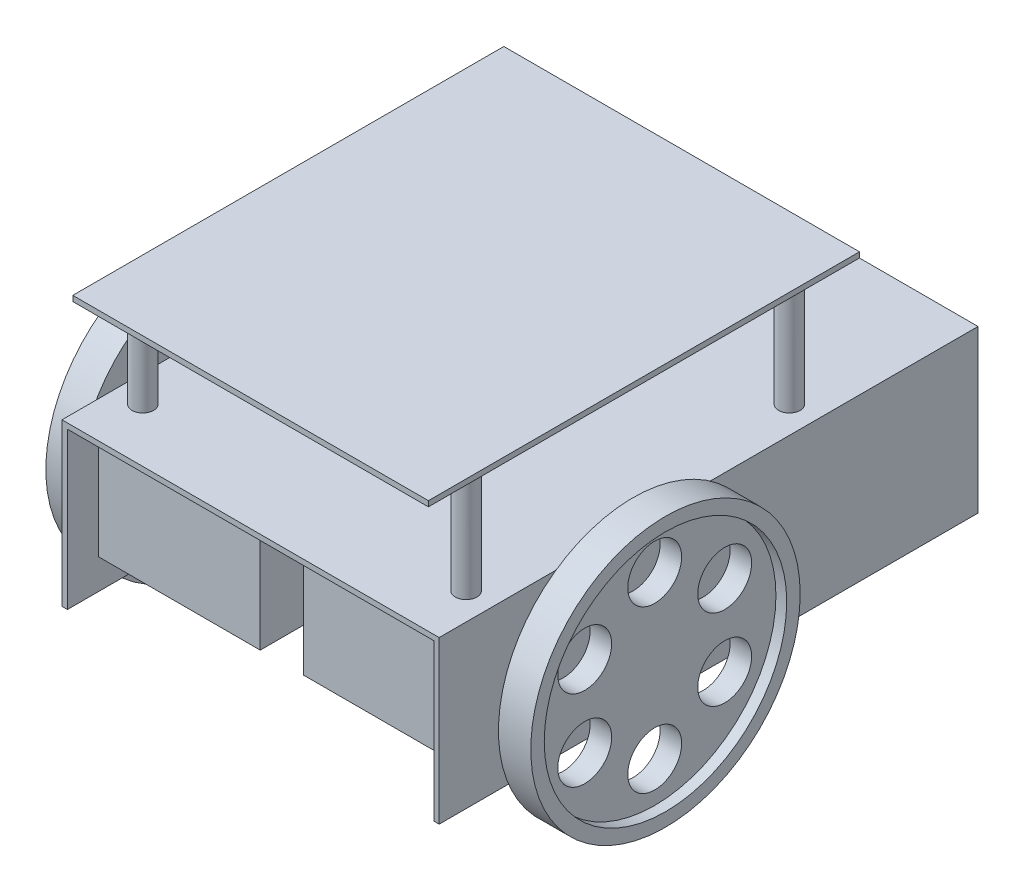
SolidWorks part; units mm, degrees
ref_plane "Front" through (0, 0, 0) normal (0, 0, 1) x (1, 0, 0)
ref_plane "Top" through (0, 0, 0) normal (0, 1, 0) x (1, 0, 0)
ref_plane "Right" through (0, 0, 0) normal (1, 0, 0) x (0, 0, -1)
sketch "草圖1" plane through (0, 0, 0) normal (0, 1, 0) x (1, 0, 0)
  line L1 (-35, 0) -> (35, 0)
  line L2 (-35, 0) -> (-35, 100)
  line L3 (-35, 100) -> (35, 100)
  line L4 (35, 0) -> (35, 100)
  dimension "D1" = 100
  dimension "D2" = 70
extrude "填料-伸長1" add sketch "草圖1" along normal blind 30
shell "薄殼1" thickness 1
sketch "草圖2" plane through (34, 0, 0) normal (-1, 0, 0) x (0, 0, 1)
  line L1 (-5.7932, 5.5786) -> (-45.7932, 5.5786)
  line L2 (-5.7932, 5.5786) -> (-5.7932, 25.5786)
  line L3 (-5.7932, 25.5786) -> (-45.7932, 25.5786)
  line L4 (-45.7932, 5.5786) -> (-45.7932, 25.5786)
  dimension "D1" = 40
  dimension "D2" = 20
extrude "填料-伸長2" add sketch "草圖2" along normal blind 30
sketch "草圖3" plane through (35, 0, 0) normal (1, 0, 0) x (0, 0, -1)
  line L0 (0, 0) -> (100, 0) construction
  line L1 (0, 30) -> (0, 0) construction
  circle A0 centre (32, 13.5) radius 1.5
  dimension "D1" = 13.5
  dimension "D2" = 32
  dimension "D3" = 3
extrude "填料-伸長3" add sketch "草圖3" along normal blind 10
sketch "草圖4" plane through (45, 0, 0) normal (1, 0, 0) x (0, 0, -1)
  circle A0 centre (32, 13.5) radius 25
  dimension "D1" = 50
extrude "填料-伸長4" add sketch "草圖4" against normal blind 6
sketch "草圖5" plane through (45, 0, 0) normal (1, 0, 0) x (0, 0, -1)
  circle A0 centre (32, 13.5) radius 22.5
  dimension "D1" = 45
extrude "除料-伸長1" cut sketch "草圖5" against normal blind 2
sketch "草圖6" plane through (43, 0, 0) normal (1, 0, 0) x (0, 0, -1)
  line L0 (32, 28.5) -> (32, 13.5) construction
  circle A0 centre (32, 28.5) radius 5
  dimension "D1" = 10
  dimension "D2" = 15
extrude "除料-伸長2" cut sketch "草圖6" against normal blind 8
pattern_circular "環狀複製排列1" count 6 over 360 about axis through (0, 13.5, -32) along (1, 0, 0) of "除料-伸長2"
mirror "鏡射1" about plane through (0, 0, 0) normal (1, 0, 0) of "填料-伸長2", "填料-伸長3", "填料-伸長4", "除料-伸長1", "除料-伸長2", "環狀複製排列1"
sketch "草圖9" plane through (0, 0, -100) normal (0, 0, -1) x (-1, 0, 0)
  line L0 (-35, 0) -> (35, 0) construction
  circle A0 centre (0, 0) radius 14
  dimension "D1" = 28
extrude "除料-伸長4" cut sketch "草圖9" against normal blind 8
sketch "草圖8" plane through (0, 0, -100) normal (0, 0, -1) x (-1, 0, 0)
  line L1 (34, 0) -> (31, 0)
  line L2 (34, 0) -> (34, 29)
  line L3 (34, 29) -> (31, 29)
  line L4 (31, 0) -> (31, 29)
  line L5 (-34, 0) -> (-31, 0)
  line L6 (-34, 0) -> (-34, 29)
  line L7 (-34, 29) -> (-31, 29)
  line L8 (-31, 0) -> (-31, 29)
  dimension "D1" = 3
  dimension "D2" = 3
extrude "除料-伸長3" cut sketch "草圖8" against normal blind 8
sketch "草圖7" plane through (0, 0, -100) normal (0, 0, -1) x (-1, 0, 0)
  line L0 (-35, 0) -> (-34, 0) construction
  line L1 (-12, 0) -> (12, 0)
  arc A0 (12, 0) -> (-12, 0) centre (0, 0) ccw
  dimension "D1" = 12
revolve "旋轉1" add sketch "草圖7" angle 360 about L1
sketch "草圖10" plane through (0, 0, 0) normal (1, 0, 0) x (0, 0, -1)
  line L0 (100, 30) -> (100, 0) construction
  circle A0 centre (100, 0) radius 1
  dimension "D1" = 2
extrude "填料-伸長5" add sketch "草圖10" along normal mid plane 28
sketch "草圖11" plane through (0, 30, 0) normal (0, 1, 0) x (1, 0, 0)
  line L0 (0, 40) -> (0, 0) construction
  line L1 (-30, 70) -> (30, 70) construction
  line L2 (-30, 70) -> (-30, 10) construction
  line L3 (-30, 10) -> (30, 10) construction
  line L4 (30, 70) -> (30, 10) construction
  line L5 (-30, 70) -> (30, 10) construction
  line L6 (-30, 10) -> (30, 70) construction
  circle A0 centre (30, 70) radius 2
  circle A1 centre (-30, 70) radius 2
  circle A2 centre (-30, 10) radius 2
  circle A3 centre (30, 10) radius 2
  point P0 (0, 40)
  dimension "D3" = 4
  dimension "D4" = 40
  dimension "D1" = 60
  dimension "D2" = 60
extrude "填料-伸長6" add sketch "草圖11" along normal blind 20
sketch "草圖12" plane through (0, 50, 0) normal (0, 1, 0) x (1, 0, 0)
  line L0 (0, 40) -> (0, 0) construction
  line L1 (-33, 80) -> (33, 80)
  line L2 (-33, 80) -> (-33, 0)
  line L3 (-33, 0) -> (33, 0)
  line L4 (33, 80) -> (33, 0)
  line L5 (-33, 80) -> (33, 0) construction
  line L6 (-33, 0) -> (33, 80) construction
  point P0 (0, 40)
  dimension "D1" = 80
  dimension "D2" = 66
  dimension "D3" = 40
extrude "填料-伸長7" add sketch "草圖12" along normal blind 1
